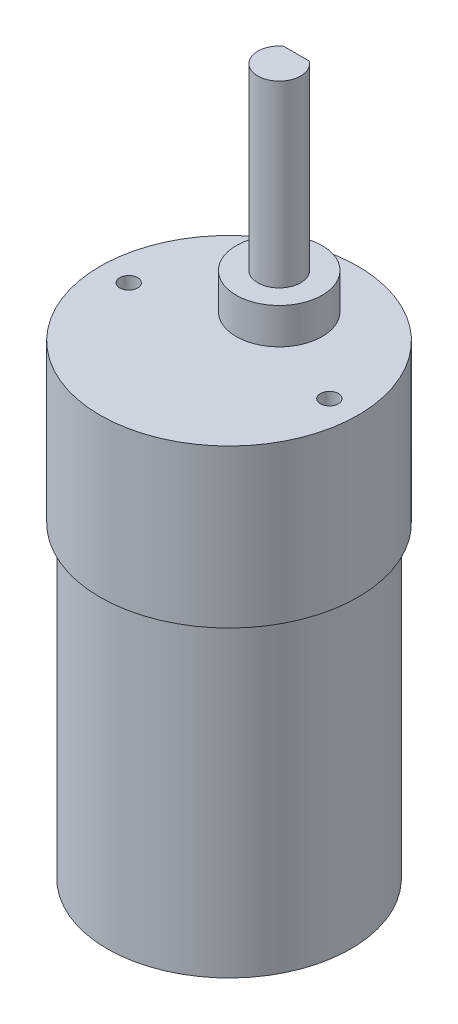
SolidWorks part; units mm, degrees
material "3.0205 (EN-AW 1200)"
ref_plane "Plan de face" through (0, 0, 0) normal (0, 0, 1) x (1, 0, 0)
ref_plane "Plan de dessus" through (0, 0, 0) normal (0, 1, 0) x (1, 0, 0)
ref_plane "Plan de droite" through (0, 0, 0) normal (1, 0, 0) x (0, 0, -1)
sketch "Esquisse1" plane through (0, 0, 0) normal (0, 1, 0) x (1, 0, 0)
  circle A0 centre (0, 0) radius 17
  dimension "D1" = 34
extrude "Boss.-Extru.1" add sketch "Esquisse1" along normal blind 43
sketch "Esquisse2" plane through (0, 43, 0) normal (0, 1, 0) x (1, 0, 0)
  circle A0 centre (0, 0) radius 18
  dimension "D1" = 36
extrude "Boss.-Extru.2" add sketch "Esquisse2" along normal blind 22
sketch "Esquisse3" plane through (0, 65, 0) normal (0, 1, 0) x (1, 0, 0)
  circle A0 centre (0, 7) radius 6
  point P2 (0, 0)
  dimension "D1" = 12
  dimension "D2" = 7
extrude "Boss.-Extru.3" add sketch "Esquisse3" along normal blind 5 contours A0
sketch "Esquisse4" plane through (0, 70, 0) normal (0, 1, 0) x (1, 0, 0)
  circle A0 centre (0, 7) radius 3
  circle A1 centre (0, 7) radius 6 construction
  dimension "D1" = 6
  dimension "D2" = 0
extrude "Boss.-Extru.4" add sketch "Esquisse4" along normal blind 25
sketch "Esquisse5" plane through (0, 65, 0) normal (0, 1, 0) x (1, 0, 0)
  circle A0 centre (14, 0) radius 1.25
  circle A1 centre (-14, 0) radius 1.25
  dimension "D1" = 28
  dimension "D2" = 2.5
  dimension "D3" = 2.5
  dimension "D4" = 14
extrude "Enlèv. mat.-Extru.1" cut sketch "Esquisse5" against normal blind 5
sketch "Esquisse6" plane through (0, 0, 0) normal (0, -1, 0) x (1, 0, 0)
  line L1 (-7.5, -7.5) -> (7.5, -7.5)
  line L2 (-7.5, -7.5) -> (-7.5, -12.5)
  line L3 (-7.5, -12.5) -> (7.5, -12.5)
  line L4 (7.5, -7.5) -> (7.5, -12.5)
  dimension "D1" = 15
  dimension "D2" = 7.5
  dimension "D3" = 5
  dimension "D4" = 7.5
extrude "Boss.-Extru.5" add sketch "Esquisse6" along normal blind 5 contours L4 L3 L2 L1
sketch "Esquisse7" plane through (0, 95, 0) normal (0, 1, 0) x (1, 0, 0)
  line L0 (-1.8, 9.4) -> (1.8, 9.4)
  circle A0 centre (0, 7) radius 3 construction
  circle A1 centre (0, 7) radius 3 construction
  arc A2 (-1.8, 9.4) -> (1.8, 9.4) centre (0, 6.9632) cw
  dimension "D1" = 2.4
extrude "Enlèv. mat.-Extru.4" cut sketch "Esquisse7" against normal blind 22 and the other way blind 10 contours A2 L0
sketch "Esquisse8" plane through (0, 0, 0) normal (0, -1, 0) x (1, 0, 0)
  circle A0 centre (0, 0) radius 5
  dimension "D1" = 10
extrude "Boss.-Extru.6" add sketch "Esquisse8" along normal blind 1
sketch "Esquisse9" plane through (0, -1, 0) normal (0, -1, 0) x (1, 0, 0)
  circle A0 centre (0, 0) radius 3.25
  dimension "D1" = 6.5
extrude "Boss.-Extru.7" add sketch "Esquisse9" along normal blind 4
